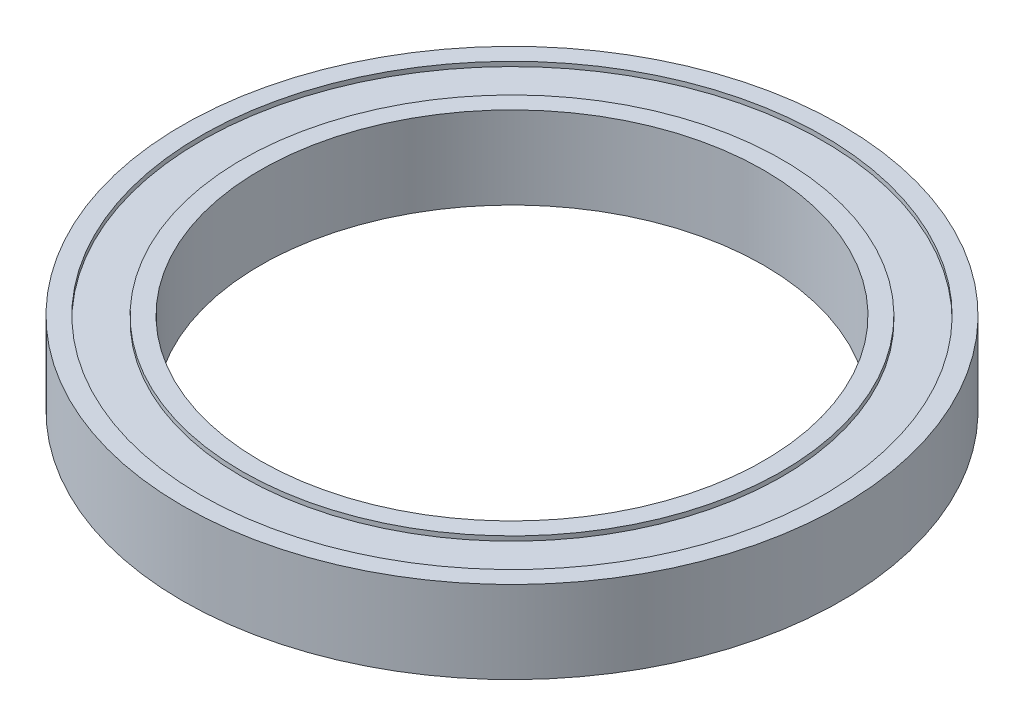
SolidWorks part; units mm, degrees
ref_plane "前视基准面" through (0, 0, 0) normal (0, 0, 1) x (1, 0, 0)
ref_plane "上视基准面" through (0, 0, 0) normal (0, 1, 0) x (1, 0, 0)
ref_plane "右视基准面" through (0, 0, 0) normal (1, 0, 0) x (0, 0, -1)
other "Configuration Table"
sketch "草图1" plane through (0, 0, 0) normal (0, 1, 0) x (1, 0, 0)
  circle A0 centre (0, 0) radius 27.5
  circle A1 centre (0, 0) radius 36
  dimension "D1" = 72
  dimension "D2" = 55
extrude "凸台-拉伸1" add sketch "草图1" along normal mid plane 9
sketch "草图3" plane through (0, 4.5, 0) normal (0, 1, 0) x (1, 0, 0)
  circle A0 centre (0, 0) radius 29.5
  circle A1 centre (0, 0) radius 34
  circle A2 centre (0, 0) radius 36 construction
  circle A3 centre (0, 0) radius 27.5 construction
  dimension "D1" = 2
  dimension "D2" = 2
extrude "切除-拉伸1" cut sketch "草图3" against normal blind 0.5
mirror "镜向1" about plane through (0, 0, 0) normal (0, 1, 0) of "切除-拉伸1"
